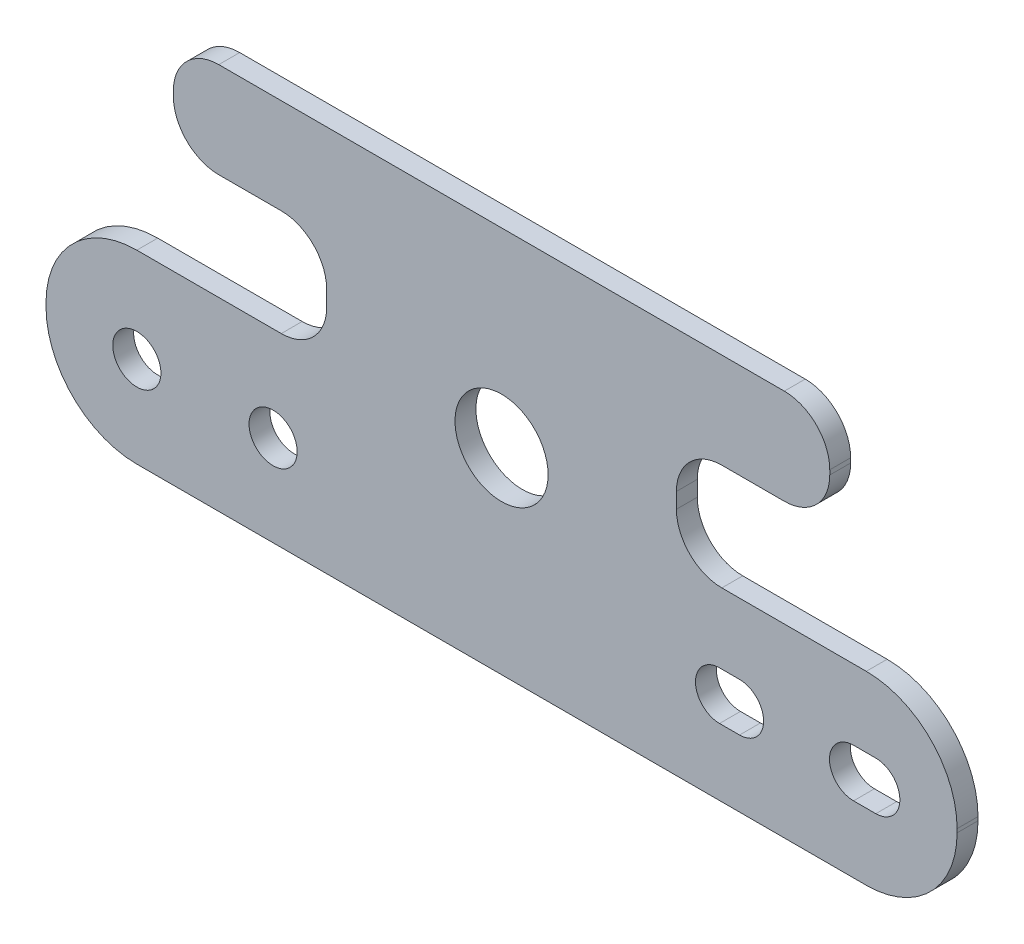
SolidWorks part; units mm, degrees
material "Alloy Steel"
ref_plane "XY" through (0, 0, 0) normal (0, 0, 1) x (1, 0, 0)
ref_plane "XZ" through (0, 0, 0) normal (0, 1, 0) x (1, 0, 0)
ref_plane "YZ" through (0, 0, 0) normal (1, 0, 0) x (0, 0, -1)
sketch "Sketch1" plane through (0, 0, 0) normal (0, 0, 1) x (1, 0, 0)
  line L0 (0, 0) -> (0, 88.926) construction
  line L1 (40.15, 0) -> (-40.15, 0)
  line L2 (-50.15, 10) -> (-50.15, 10.4)
  line L3 (-40.15, 20.4) -> (-24.25, 20.4)
  line L4 (-19.25, 25.4) -> (-19.25, 27.1)
  line L5 (-24.25, 32.1) -> (-31.13, 32.1)
  line L6 (-36.13, 37.1) -> (-36.13, 37.6)
  line L7 (-31.13, 42.6) -> (31.13, 42.6)
  line L8 (36.13, 37.1) -> (36.13, 37.6)
  line L9 (24.25, 32.1) -> (31.13, 32.1)
  line L10 (19.25, 25.4) -> (19.25, 27.1)
  line L11 (40.15, 20.4) -> (24.25, 20.4)
  line L12 (50.15, 10) -> (50.15, 10.4)
  arc A0 (-31.13, 32.1) -> (-36.13, 37.1) centre (-31.13, 37.1) cw
  arc A1 (-36.13, 37.6) -> (-31.13, 42.6) centre (-31.13, 37.6) cw
  arc A2 (-50.15, 10.4) -> (-40.15, 20.4) centre (-40.15, 10.4) cw
  arc A3 (-50.15, 10) -> (-40.15, 0) centre (-40.15, 10) ccw
  arc A4 (-19.25, 27.1) -> (-24.25, 32.1) centre (-24.25, 27.1) ccw
  arc A5 (-24.25, 20.4) -> (-19.25, 25.4) centre (-24.25, 25.4) ccw
  arc A6 (24.25, 20.4) -> (19.25, 25.4) centre (24.25, 25.4) cw
  arc A7 (19.25, 27.1) -> (24.25, 32.1) centre (24.25, 27.1) cw
  arc A8 (36.13, 37.6) -> (31.13, 42.6) centre (31.13, 37.6) ccw
  arc A9 (31.13, 32.1) -> (36.13, 37.1) centre (31.13, 37.1) ccw
  arc A10 (50.15, 10.4) -> (40.15, 20.4) centre (40.15, 10.4) ccw
  arc A11 (50.15, 10) -> (40.15, 0) centre (40.15, 10) cw
  point P13 (-36.13, 32.1)
  point P16 (-36.13, 42.6)
  point P20 (-50.15, 0)
  point P23 (-19.25, 32.1)
  point P26 (-19.25, 20.4)
  point P39 (0, 42.6)
  point P42 (19.25, 20.4)
  point P43 (19.25, 32.1)
  point P44 (50.15, 0)
  point P45 (36.13, 42.6)
  point P46 (36.13, 32.1)
  dimension "D7" = 5
  dimension "D8" = 10
  dimension "D9" = 5
  dimension "D1" = 20.4
  dimension "D2" = 30.9
  dimension "D3" = 50.15
  dimension "D4" = 11.7
  dimension "D5" = 10.5
  dimension "D6" = 36.13
extrude "Boss-Extrude1" add sketch "Sketch1" along normal blind 2.3
sketch "Sketch2" plane through (0, 0, 2.3) normal (0, 0, 1) x (1, 0, 0)
  line L0 (-50.1508, 10) -> (50.15, 10) construction
  line L1 (23.9992, 10) -> (26.1992, 10) construction
  line L4 (23.9992, 12.65) -> (26.1992, 12.65)
  line L5 (23.9992, 7.35) -> (26.1992, 7.35)
  line L6 (38.7492, 10) -> (41.1992, 10) construction
  line L7 (38.7492, 12.65) -> (41.1992, 12.65)
  line L8 (38.7492, 7.35) -> (41.1992, 7.35)
  line L9 (0, 0) -> (0, 42.6) construction
  line L10 (31.13, 42.6) -> (-31.13, 42.6) construction
  circle A0 centre (-40.1508, 10) radius 2.65
  circle A1 centre (-25.1508, 10) radius 2.65
  arc A4 (23.9992, 12.65) -> (23.9992, 7.35) centre (23.9992, 10) ccw
  arc A5 (26.1992, 7.35) -> (26.1992, 12.65) centre (26.1992, 10) ccw
  arc A6 (38.7492, 12.65) -> (38.7492, 7.35) centre (38.7492, 10) ccw
  arc A7 (41.1992, 7.35) -> (41.1992, 12.65) centre (41.1992, 10) ccw
  circle A8 centre (0, 21.625) radius 5.125
  point P4 (-40.1508, 10)
  point P5 (-25.1508, 10)
  point P10 (23.9992, 10)
  point P11 (26.1992, 10)
  point P14 (25.0992, 10)
  point P19 (38.7492, 10)
  point P20 (41.1992, 10)
  point P21 (39.9742, 10)
  dimension "D3" = 74.15
  dimension "D9" = 21.625
  dimension "D1" = 10
  dimension "D2" = 25
  dimension "D4" = 76.35
  dimension "D5" = 5.3
  dimension "D6" = 88.9
  dimension "D7" = 91.35
  dimension "D8" = 5.3
extrude "Cut-Extrude1" cut sketch "Sketch2" against normal up to next
